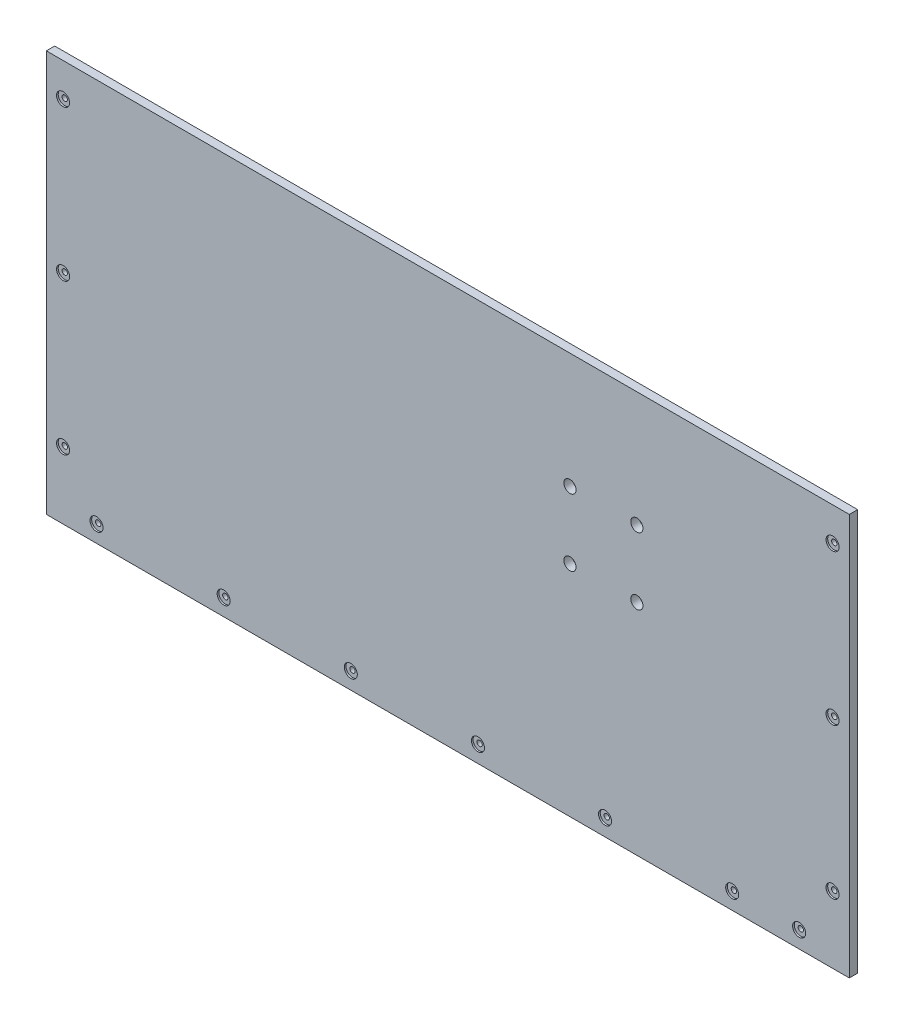
SolidWorks part; units mm, degrees
ref_plane "Front Plane" through (0, 0, 0) normal (0, 0, 1) x (1, 0, 0)
ref_plane "Top Plane" through (0, 0, 0) normal (0, 1, 0) x (1, 0, 0)
ref_plane "Right Plane" through (0, 0, 0) normal (1, 0, 0) x (0, 0, -1)
sketch "Sketch1" plane through (0, 0, 0) normal (0, 0, 1) x (1, 0, 0)
  line L1 (0, 0) -> (-609.6, 0)
  line L2 (0, 0) -> (0, 304.8)
  line L3 (0, 304.8) -> (-609.6, 304.8)
  line L4 (-609.6, 0) -> (-609.6, 304.8)
  dimension "D1" = 304.8
  dimension "D2" = 609.6
extrude "Boss-Extrude1" add sketch "Sketch1" along normal blind 6.35
sketch "Sketch2" plane through (0, 0, 6.35) normal (0, 0, 1) x (1, 0, 0)
  line L0 (0, 0) -> (0, 304.8) construction
  line L1 (-218.44, 223.52) -> (-154.94, 223.52) construction
  line L2 (-218.44, 223.52) -> (-218.44, 160.02) construction
  line L3 (-218.44, 160.02) -> (-154.94, 160.02) construction
  line L4 (-154.94, 223.52) -> (-154.94, 160.02) construction
  line L5 (-218.44, 223.52) -> (-154.94, 160.02) construction
  line L6 (-218.44, 160.02) -> (-154.94, 223.52) construction
  line L7 (0, 304.8) -> (-609.6, 304.8) construction
  line L8 (-186.69, 223.52) -> (-186.69, 160.02) construction
  line L9 (-218.44, 191.77) -> (-154.94, 191.77) construction
  circle A0 centre (-161.29, 217.17) radius 4.6355
  circle A1 centre (-212.09, 217.17) radius 4.6355
  circle A2 centre (-161.29, 166.37) radius 4.6355
  circle A3 centre (-212.09, 166.37) radius 4.6355
  point P2 (-186.69, 191.77)
  dimension "D1" = 9.271
  dimension "D2" = 63.5
  dimension "D3" = 63.5
  dimension "D4" = 6.35
  dimension "D5" = 186.69
  dimension "D6" = 113.03
extrude "Cut-Extrude1" cut sketch "Sketch2" against normal through all
sketch "Sketch3" plane through (0, 0, 6.35) normal (0, 0, 1) x (1, 0, 0)
  line L0 (-609.6, 304.8) -> (-609.6, 0) construction
  line L1 (0, 304.8) -> (-609.6, 304.8) construction
  line L2 (-304.8, 304.8) -> (-304.8, 0) construction
  line L3 (-609.6, 0) -> (0, 0) construction
  circle A0 centre (-596.9, 279.4) radius 2.032
  circle A1 centre (-596.9, 165.1) radius 2.032
  circle A2 centre (-596.9, 50.8) radius 2.032
  circle A3 centre (-12.7, 50.8) radius 2.032
  circle A4 centre (-12.7, 165.1) radius 2.032
  circle A5 centre (-12.7, 279.4) radius 2.032
  dimension "D1" = 4.064
  dimension "D2" = 12.7
  dimension "D3" = 25.4
  dimension "D5" = 114.3
  dimension "D4" = 3
extrude "Cut-Extrude2" cut sketch "Sketch3" against normal through all
sketch "Sketch5" plane through (0, 0, 6.35) normal (0, 0, 1) x (1, 0, 0)
  line L0 (-609.6, 0) -> (0, 0) construction
  line L1 (-609.6, 304.8) -> (-609.6, 0) construction
  line L2 (-304.8, 304.8) -> (-304.8, 0) construction
  line L3 (0, 304.8) -> (-609.6, 304.8) construction
  circle A0 centre (-571.5, 12.7) radius 2.032
  circle A1 centre (-38.1, 12.7) radius 2.032
  circle A2 centre (-474.98, 12.7) radius 2.032
  circle A3 centre (-378.46, 12.7) radius 2.032
  circle A4 centre (-281.94, 12.7) radius 2.032
  circle A5 centre (-185.42, 12.7) radius 2.032
  circle A6 centre (-88.9, 12.7) radius 2.032
  dimension "D1" = 4.064
  dimension "D2" = 12.7
  dimension "D3" = 38.1
  dimension "D5" = 96.52
  dimension "D4" = 6
extrude "Cut-Extrude3" cut sketch "Sketch5" against normal through all
sketch "Sketch6" plane through (0, 0, 6.35) normal (0, 0, 1) x (1, 0, 0)
  line L0 (-304.8, 304.8) -> (-304.8, 0) construction
  line L1 (0, 304.8) -> (-609.6, 304.8) construction
  line L2 (-609.6, 0) -> (0, 0) construction
  circle A0 centre (-596.9, 279.4) radius 4.953
  circle A1 centre (-596.9, 165.1) radius 4.953
  circle A2 centre (-596.9, 50.8) radius 4.953
  circle A3 centre (-12.7, 50.8) radius 4.953
  circle A4 centre (-12.7, 165.1) radius 4.953
  circle A5 centre (-12.7, 279.4) radius 4.953
  dimension "D1" = 9.906
  dimension "D3" = 114.3
  dimension "D2" = 3
extrude "Cut-Extrude4" cut sketch "Sketch6" against normal blind 1.27
sketch "Sketch7" plane through (0, 0, 6.35) normal (0, 0, 1) x (1, 0, 0)
  line L0 (-304.8, 304.8) -> (-304.8, 0) construction
  line L1 (0, 304.8) -> (-609.6, 304.8) construction
  line L2 (-609.6, 0) -> (0, 0) construction
  circle A0 centre (-571.5, 12.7) radius 4.953
  circle A1 centre (-474.98, 12.7) radius 4.953
  circle A2 centre (-378.46, 12.7) radius 4.953
  circle A3 centre (-281.94, 12.7) radius 4.953
  circle A4 centre (-185.42, 12.7) radius 4.953
  circle A5 centre (-88.9, 12.7) radius 4.953
  circle A6 centre (-38.1, 12.7) radius 4.953
  dimension "D1" = 9.906
  dimension "D3" = 96.52
  dimension "D2" = 6
extrude "Cut-Extrude5" cut sketch "Sketch7" against normal blind 1.27
equation "\"D6@Sketch2\"=1.5+2.95in"
